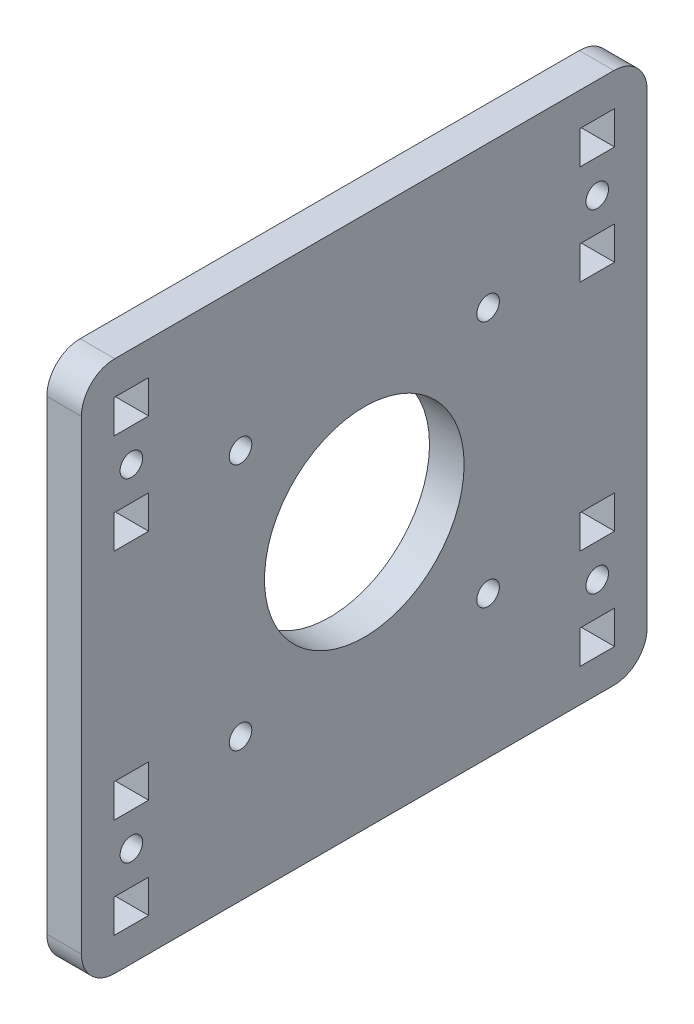
SolidWorks part; units mm, degrees
material "Acrylic (Blue)"
ref_plane "Front Plane" through (0, 0, 0) normal (0, 0, 1) x (1, 0, 0)
ref_plane "Top Plane" through (0, 0, 0) normal (0, 1, 0) x (1, 0, 0)
ref_plane "Right Plane" through (0, 0, 0) normal (1, 0, 0) x (0, 0, -1)
sketch "Sketch1" plane through (0, 0, 0) normal (1, 0, 0) x (0, 0, -1)
  line L0 (44.45, 0) -> (-44.45, 0) construction
  line L1 (-53.975, 50.8) -> (53.975, 50.8)
  line L2 (-53.975, 50.8) -> (-53.975, -50.8)
  line L3 (-53.975, -50.8) -> (53.975, -50.8)
  line L4 (53.975, 50.8) -> (53.975, -50.8)
  line L5 (-53.975, 50.8) -> (53.975, -50.8) construction
  line L6 (-53.975, -50.8) -> (53.975, 50.8) construction
  line L7 (-44.45, 31.75) -> (-44.45, -31.75) construction
  line L8 (44.45, 31.75) -> (44.45, -31.75) construction
  circle A0 centre (0, 0) radius 19.05
  point P0 (0, 0)
  line B0 (-47.752, 38.1) -> (-47.752, 44.45)
  line B1 (-47.752, 44.45) -> (-41.148, 44.45)
  line B2 (-41.148, 44.45) -> (-41.148, 38.1)
  line B3 (-41.148, 38.1) -> (-47.752, 38.1)
  line B4 (-47.752, 19.05) -> (-47.752, 25.4)
  line B5 (-47.752, 25.4) -> (-41.148, 25.4)
  line B6 (-41.148, 25.4) -> (-41.148, 19.05)
  line B7 (-41.148, 19.05) -> (-47.752, 19.05)
  circle B8 centre (-44.45, 31.75) radius 2.1526
  line B9 (-47.752, -25.4) -> (-47.752, -19.05)
  line B10 (-47.752, -19.05) -> (-41.148, -19.05)
  line B11 (-41.148, -19.05) -> (-41.148, -25.4)
  line B12 (-41.148, -25.4) -> (-47.752, -25.4)
  line B13 (-47.752, -44.45) -> (-47.752, -38.1)
  line B14 (-47.752, -38.1) -> (-41.148, -38.1)
  line B15 (-41.148, -38.1) -> (-41.148, -44.45)
  line B16 (-41.148, -44.45) -> (-47.752, -44.45)
  circle B17 centre (-44.45, -31.75) radius 2.1526
  line B18 (41.148, 38.1) -> (41.148, 44.45)
  line B19 (41.148, 44.45) -> (47.752, 44.45)
  line B20 (47.752, 44.45) -> (47.752, 38.1)
  line B21 (47.752, 38.1) -> (41.148, 38.1)
  line B22 (41.148, 19.05) -> (41.148, 25.4)
  line B23 (41.148, 25.4) -> (47.752, 25.4)
  line B24 (47.752, 25.4) -> (47.752, 19.05)
  line B25 (47.752, 19.05) -> (41.148, 19.05)
  circle B26 centre (44.45, 31.75) radius 2.1526
  line B27 (47.752, -38.1) -> (47.752, -44.45)
  line B28 (47.752, -44.45) -> (41.148, -44.45)
  line B29 (41.148, -44.45) -> (41.148, -38.1)
  line B30 (41.148, -38.1) -> (47.752, -38.1)
  line B31 (47.752, -19.05) -> (47.752, -25.4)
  line B32 (47.752, -25.4) -> (41.148, -25.4)
  line B33 (41.148, -25.4) -> (41.148, -19.05)
  line B34 (41.148, -19.05) -> (47.752, -19.05)
  circle B35 centre (44.45, -31.75) radius 2.1526
  dimension "D1" = 101.6
  dimension "D3" = 38.1
  dimension "D5" = 63.5
  dimension "D2" = 107.95
  dimension "D4" = 9.525
sketch_block_instance "BOLT_HOLE-1"
sketch_block "BOLT_HOLE" parameters "D1"=4.3053, "D2"=6.35, "D3"=6.35, "D4"=6.604
sketch_block_instance "BOLT_HOLE-2"
sketch_block_instance "BOLT_HOLE-3"
sketch_block_instance "BOLT_HOLE-4"
extrude "Boss-Extrude1" add sketch "Sketch1" along normal blind 6.604
hole_wizard "#10-32 Tapped Hole1" positions "Sketch7" profile "Sketch6" tap size "#10-32" standard "ANSI Inch"
sketch "Sketch7" plane through (6.604, 0, 0) normal (1, 0, 0) x (0, 0, -1)
  line L12 (-23.622, -23.622) -> (23.622, -23.622) construction
  line L13 (23.622, -23.622) -> (23.622, 23.622) construction
  line L14 (23.622, 23.622) -> (23.7179, 23.622) construction
  line L15 (-23.622, 23.622) -> (23.622, 23.622) construction
  line L17 (-23.622, 23.622) -> (-23.622, -23.622) construction
  line L21 (0, 50.8) -> (0, 23.622) construction
  line L22 (53.975, 50.8) -> (-53.975, 50.8) construction
  line L23 (0, 23.622) -> (0, -23.622) construction
  line L24 (0, -23.622) -> (0, -50.8) construction
  line L26 (-53.975, -50.8) -> (53.975, -50.8) construction
  point P0 (-23.622, 23.622)
  point P2 (23.622, 23.622)
  point P4 (-23.622, -23.622)
  point P6 (23.622, -23.622)
  dimension "D1" = 47.244
sketch "Sketch6" plane through (6.604, 23.622, 23.622) normal (0, 1, 0) x (0, 0, -1)
  line L0 (0, 0) -> (0, 13.2529)
  line L1 (0, 13.2529) -> (2.0193, 12.0396)
  line L2 (2.0193, 12.0396) -> (2.0193, 0)
  line L5 (2.0193, 0) -> (0, 0)
  line L10 (0, 13.2529) -> (-2.0193, 12.0396) construction
  line L11 (0, -6.35) -> (0, 107.95) construction
  dimension "Tap Drill Dia." = 4.0386
  dimension "Tap Drill Depth" = 12.0396
  dimension "Drill Angle" = 118
fillet "Fillet1" radius 6.35 4 edges at (3.302, 50.8, 53.975) (3.302, -50.8, 53.975) (3.302, -50.8, -53.975) (3.302, 50.8, -53.975)
other "Move Face1" [suppressed] parameters "D1"=0.0508
hole_wizard "CSK for #8 Flat Head Socket Cap Screw2" positions "Sketch11" profile "Sketch10" countersink size "#8" standard "ANSI Inch" end condition through all
sketch "Sketch11" plane through (0, 0, 0) normal (-1, 0, 0) x (0, 0, 1)
  point P0 (-44.45, 31.75)
  point P3 (-23.622, 23.622)
  point P6 (23.622, 23.622)
  point P9 (44.45, 31.75)
  point P12 (23.622, -23.622)
  point P15 (-23.622, -23.622)
  point P18 (-44.45, -31.75)
  point P21 (44.45, -31.75)
sketch "Sketch10" plane through (0, 31.75, -44.45) normal (0, 1, 0) x (0, 0, 1)
  line L0 (0, 0) -> (0, 6.604)
  line L1 (0, 6.604) -> (2.1526, 6.604)
  line L2 (2.1526, 6.604) -> (2.1526, 2.7685)
  line L3 (2.1526, 2.7685) -> (4.5593, 0)
  line L5 (4.5593, 0) -> (0, 0)
  line L6 (-2.1526, 2.7685) -> (-4.5593, 0) construction
  line L11 (0, -6.35) -> (0, 107.95) construction
  dimension "Thru Hole Dia." = 4.3053
  dimension "Thru Hole Depth" = 6.604
  dimension "Near C'Sink Dia." = 9.1186
  dimension "Near C'Sink Angle" = 82
